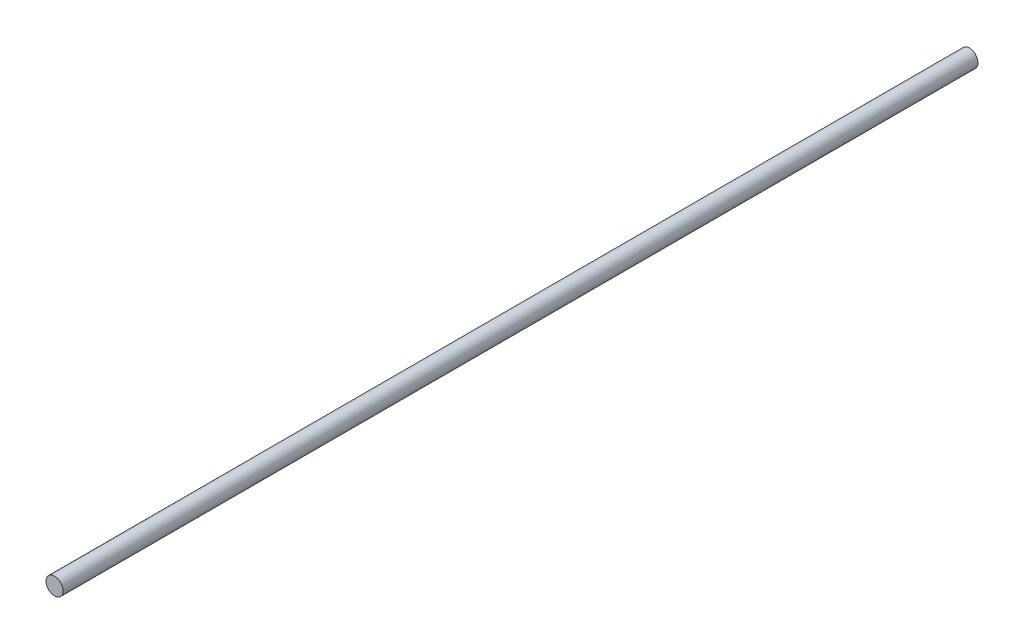
SolidWorks part; units mm, degrees
ref_plane "Front Plane" through (0, 0, 0) normal (0, 0, 1) x (1, 0, 0)
ref_plane "Top Plane" through (0, 0, 0) normal (0, 1, 0) x (1, 0, 0)
ref_plane "Right Plane" through (0, 0, 0) normal (1, 0, 0) x (0, 0, -1)
sketch "Sketch1" plane through (0, 0, 0) normal (0, 0, 1) x (1, 0, 0)
  circle A0 centre (0, 0) radius 4.765
  dimension "D1" = 9.53
extrude "Boss-Extrude1" add sketch "Sketch1" along normal mid plane 508
